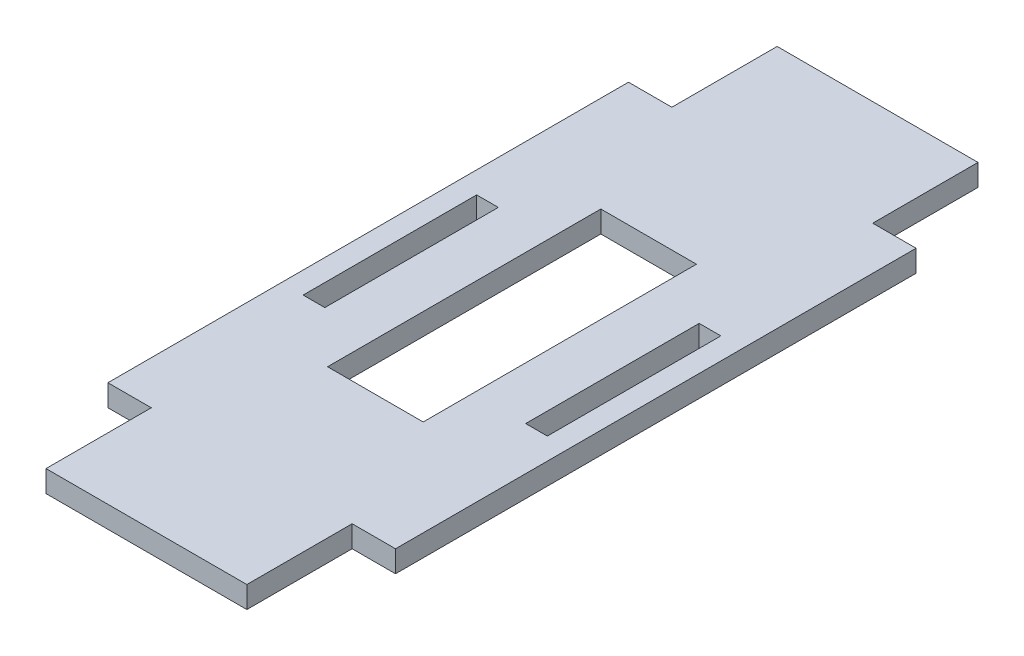
SolidWorks part; units mm, degrees
ref_plane "Front Plane" through (0, 0, 0) normal (0, 0, 1) x (1, 0, 0)
ref_plane "Top Plane" through (0, 0, 0) normal (0, 1, 0) x (1, 0, 0)
ref_plane "Right Plane" through (0, 0, 0) normal (1, 0, 0) x (0, 0, -1)
sketch "Sketch1" plane through (0, 0, 0) normal (0, 1, 0) x (1, 0, 0)
  line L24 (-14.7, -53.5129) -> (14.7, -53.5129)
  line L25 (14.7, -53.5129) -> (14.7, -38.1)
  line L26 (14.7, -38.1) -> (17.875, -38.1)
  line L27 (17.875, -38.1) -> (17.875, -12.7)
  line L28 (17.875, -12.7) -> (14.7, -12.7)
  line L29 (14.7, -12.7) -> (14.7, 12.7)
  line L30 (14.7, 12.7) -> (17.875, 12.7)
  line L31 (17.875, 12.7) -> (17.875, 38.1)
  line L32 (17.875, 38.1) -> (14.7, 38.1)
  line L33 (14.7, 38.1) -> (14.7, 53.5129)
  line L34 (14.7, 53.5129) -> (-14.7, 53.5129)
  line L35 (-14.7, 53.5129) -> (-14.7, 38.1)
  line L36 (-14.7, 38.1) -> (-17.875, 38.1)
  line L37 (-17.875, 38.1) -> (-17.875, 12.7)
  line L38 (-17.875, 12.7) -> (-14.7, 12.7)
  line L39 (-14.7, 12.7) -> (-14.7, -12.7)
  line L40 (-14.7, -12.7) -> (-17.875, -12.7)
  line L41 (-17.875, -12.7) -> (-17.875, -38.1)
  line L42 (-17.875, -38.1) -> (-14.7, -38.1)
  line L43 (-14.7, -38.1) -> (-14.7, -53.5129)
  line L44 (-17.875, -12.7) -> (-17.875, 12.7) construction
  line L46 (-7, -20) -> (7, -20)
  line L47 (-7, -20) -> (-7, 20)
  line L48 (-7, 20) -> (7, 20)
  line L49 (7, -20) -> (7, 20)
  line L50 (-7, -20) -> (7, 20) construction
  line L51 (-7, 20) -> (7, -20) construction
  line L52 (17.875, 38.1) -> (21.05, 38.1)
  line L53 (17.875, 38.1) -> (17.875, -38.1)
  line L54 (17.875, -38.1) -> (21.05, -38.1)
  line L55 (21.05, 38.1) -> (21.05, -38.1)
  line L56 (-17.875, 38.1) -> (-21.05, 38.1)
  line L57 (-17.875, 38.1) -> (-17.875, -38.1)
  line L58 (-17.875, -38.1) -> (-21.05, -38.1)
  line L59 (-21.05, 38.1) -> (-21.05, -38.1)
  point P20 (0, -53.5128)
  point P21 (0, 53.5129)
  point P22 (0, 0)
  point P23 (14.7, 0)
  dimension "D1" = 25.4
  dimension "D2" = 29.4
  dimension "D3" = 3.175
  dimension "D4" = 107.0257
  dimension "D5" = 14
  dimension "D6" = 40
extrude "Boss-Extrude1" add sketch "Sketch1" along normal blind 3.175 contours L42 L43 L24 L25 L26 L27 L28 L29 L30 L31 L32 L33 L34 L35 L36 L37 L38 L39 L40 L41 L49 L46 L47 L48 | L56 L59 L58 L41 L57 L37 | L55 L52 L31 L53 L27 L54
